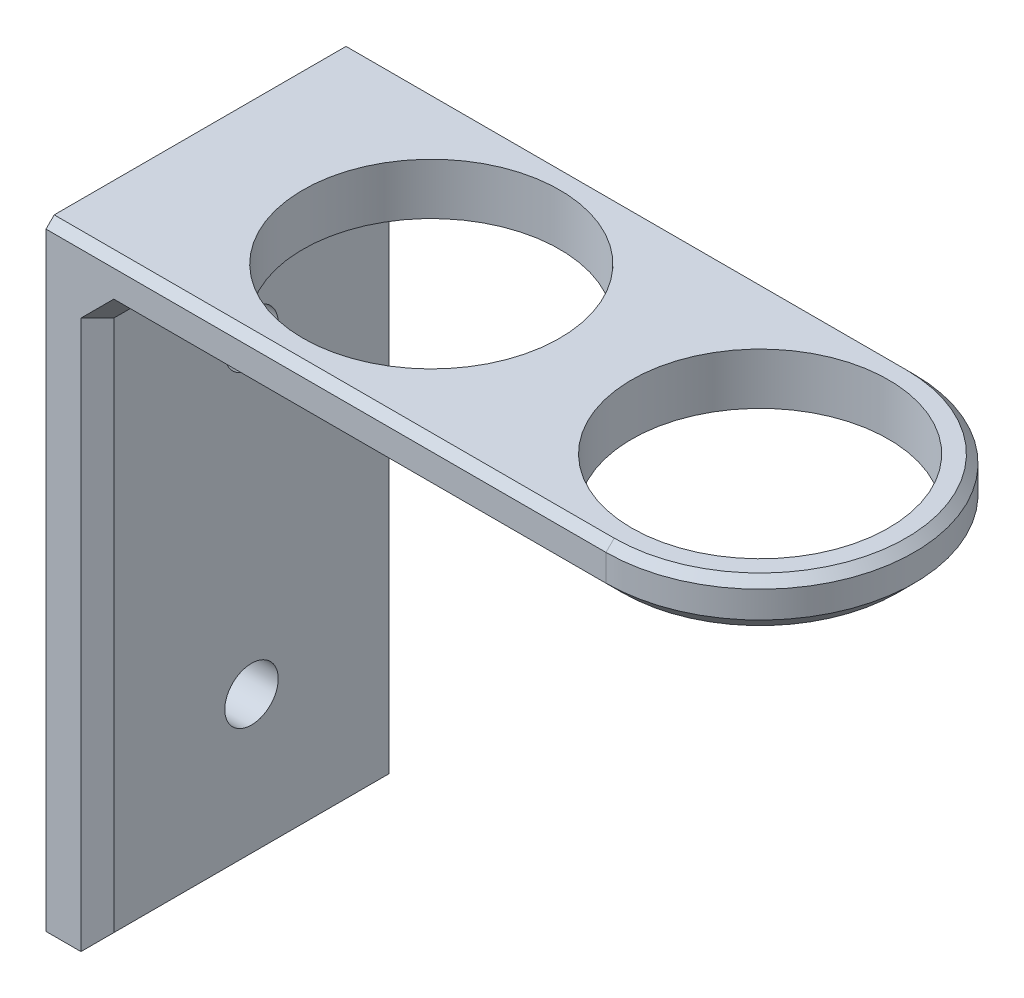
SolidWorks part; units mm, degrees
ref_plane "Front Plane" through (0, 0, 0) normal (0, 0, 1) x (1, 0, 0)
ref_plane "Top Plane" through (0, 0, 0) normal (0, 1, 0) x (1, 0, 0)
ref_plane "Right Plane" through (0, 0, 0) normal (1, 0, 0) x (0, 0, -1)
sketch "Sketch1" plane through (0, 0, 0) normal (1, 0, 0) x (0, 0, -1)
  line L0 (0, 0) -> (-38.1, 0)
  line L1 (-38.1, 0) -> (-38.1, -38.1)
  line L2 (-38.1, -38.1) -> (0, -38.1)
  line L3 (0, -38.1) -> (0, 0)
  line L4 (0, 0) -> (0, 38.1)
  line L5 (0, 38.1) -> (-38.1, 38.1)
  line L6 (-38.1, 38.1) -> (-38.1, 0)
  line L7 (-38.1, -19.05) -> (0, -19.05) construction
  circle A0 centre (-19.05, -19.05) radius 3.302 construction
extrude "Boss-Extrude1" add sketch "Sketch1" along normal blind 6.35 contours L5 L6 L0 L4 | L2 L3 L0 L1
sketch "Sketch2" plane through (6.35, 0, 0) normal (1, 0, 0) x (0, 0, -1)
  line L0 (-38.1, -19.05) -> (0, -19.05) construction
  circle A0 centre (-19.05, -19.05) radius 3.302
extrude "Cut-Extrude1" cut sketch "Sketch2" against normal up to surface (6.35 mm away) up to face at (0, 0, 19.05)
sketch "Sketch3" plane through (6.35, 0, 0) normal (1, 0, 0) x (0, 0, -1)
  line L0 (-19.05, 38.1) -> (-19.05, 0) construction
  line L1 (0, 38.1) -> (-38.1, 38.1) construction
  line L2 (0, 0) -> (-38.1, 0) construction
  circle A0 centre (-19.05, 19.05) radius 3.302
extrude "Cut-Extrude2" cut sketch "Sketch3" against normal up to surface (6.35 mm away) up to face at (0, -19.05, 15.748)
sketch "Sketch4" plane through (0, 38.1, 0) normal (0, 1, 0) x (1, 0, 0)
  line L0 (6.35, -19.05) -> (12.7, -19.05) construction
  line L1 (6.35, 0) -> (6.35, -38.1) construction
  line L2 (12.7, -19.05) -> (44.45, -19.05) construction
  line L3 (44.45, -19.05) -> (53.34, -19.05) construction
  line L4 (53.34, -19.05) -> (85.09, -19.05) construction
  line L5 (28.575, 0) -> (28.575, -38.1) construction
  line L6 (69.215, -38.1) -> (69.215, 0) construction
  line L7 (6.35, 0) -> (28.575, 0)
  line L8 (28.575, 0) -> (69.215, 0)
  line L9 (6.35, -38.1) -> (28.575, -38.1)
  line L10 (28.575, -38.1) -> (69.215, -38.1)
  circle A1 centre (28.575, -19.05) radius 15.875
  circle A2 centre (69.215, -19.05) radius 15.875
  arc A3 (69.215, 0) -> (69.215, -38.1) centre (69.215, -19.05) cw
  point P14 (28.575, -19.05)
  point P16 (69.215, -19.05)
  line M7 (6.35, -38.1) -> (6.35, 0)
  dimension "D2" = 6.35
  dimension "D1" = 31.75
  dimension "D3" = 31.75
  dimension "D4" = 8.89
extrude "Boss-Extrude2" add sketch "Sketch4" against normal blind 6.35 contours A3 L8 L7 L9 L10 A2 A1 M7
chamfer "Chamfer1" distance 2.032 7 edges at (88.265, 31.75, 19.05) (37.7825, 31.75, 0) (37.7825, 31.75, 38.1) (6.35, -38.1, 19.05) (6.35, -3.175, 0) (6.35, -3.175, 38.1) (6.35, 31.75, 19.05)
chamfer "Chamfer2" distance 1.016 angle 45 3 edges at (34.6075, 38.1, 0) (88.265, 38.1, 19.05) (34.6075, 38.1, 38.1)
